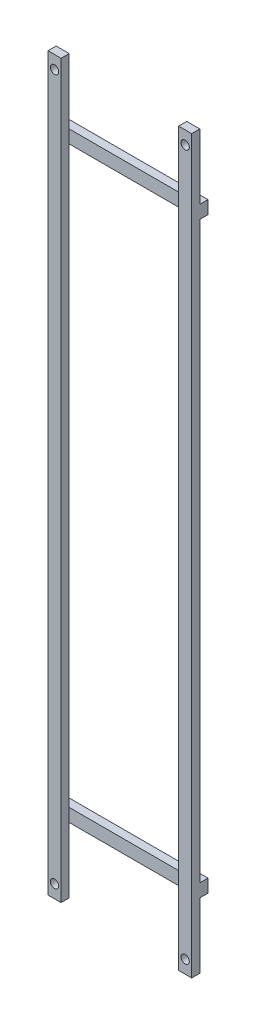
SolidWorks part; units mm, degrees
ref_plane "Front Plane" through (0, 0, 0) normal (0, 0, 1) x (1, 0, 0)
ref_plane "Top Plane" through (0, 0, 0) normal (0, 1, 0) x (1, 0, 0)
ref_plane "Right Plane" through (0, 0, 0) normal (1, 0, 0) x (0, 0, -1)
ref_plane "Plane1" through (45, 0, 0) normal (-1, 0, 0) x (0, -1, 0)
sketch "Sketch1" plane through (45, 0, 0) normal (-1, 0, 0) x (0, -1, 0)
  line L0 (-37.6165, 80) -> (-37.6165, 0)
  line L1 (-37.6165, 0) -> (472.3835, 0)
  line L2 (472.3835, 0) -> (472.3835, 80)
  line L3 (472.3835, 80) -> (-37.6165, 80)
extrude "Boss-Extrude1" add sketch "Sketch1" against normal blind 10
sketch "Sketch2" plane through (45, 0, 0) normal (-1, 0, 0) x (0, 0, 1)
  line L0 (0, -22.3835) -> (0, -412.3835)
  line L1 (0, -412.3835) -> (70, -412.3835)
  line L2 (70, -412.3835) -> (70, -22.3835)
  line L3 (70, -22.3835) -> (0, -22.3835)
extrude "Cut-Extrude1" cut sketch "Sketch2" against normal through all
sketch "Sketch3" plane through (45, 0, 0) normal (-1, 0, 0) x (0, 0, 1)
  line L0 (0, -12.3835) -> (70, -12.3835)
  line L1 (70, -12.3835) -> (70, 37.6165)
  line L2 (70, 37.6165) -> (0, 37.6165)
  line L3 (0, 37.6165) -> (0, -12.3835)
extrude "Cut-Extrude2" cut sketch "Sketch3" against normal through all
sketch "Sketch4" plane through (45, 0, 0) normal (-1, 0, 0) x (0, 0, 1)
  line L0 (70, -22.3835) -> (0, -22.3835)
  line L1 (0, -22.3835) -> (0, -12.3835)
  line L2 (0, -12.3835) -> (70, -12.3835)
  line L3 (70, -12.3835) -> (70, -22.3835)
extrude "Boss-Extrude2" add sketch "Sketch4" along normal blind 100
sketch "Sketch5" plane through (45, 0, 0) normal (-1, 0, 0) x (0, 0, 1)
  line L0 (70, -472.3835) -> (70, -422.3835)
  line L1 (70, -422.3835) -> (0, -422.3835)
  line L2 (0, -422.3835) -> (0, -472.3835)
  line L3 (0, -472.3835) -> (70, -472.3835)
extrude "Cut-Extrude3" cut sketch "Sketch5" against normal through all
sketch "Sketch6" plane through (45, 0, 0) normal (-1, 0, 0) x (0, 0, 1)
  line L0 (70, -422.3835) -> (0, -422.3835)
  line L1 (0, -422.3835) -> (0, -412.3835)
  line L2 (0, -412.3835) -> (70, -412.3835)
  line L3 (70, -412.3835) -> (70, -422.3835)
extrude "Boss-Extrude3" add sketch "Sketch6" along normal blind 100
sketch "Sketch7" plane through (0, 0, 70) normal (0, 0, 1) x (1, 0, 0)
  line L0 (-45, -12.3835) -> (-45, -472.3835)
  line L1 (-45, -472.3835) -> (-55, -472.3835)
  line L2 (-55, -472.3835) -> (-55, -12.3835)
  line L3 (-55, -12.3835) -> (-45, -12.3835)
extrude "Boss-Extrude4" add sketch "Sketch7" along normal blind 10
sketch "Sketch8" plane through (0, -12.3835, 0) normal (0, 1, 0) x (-1, 0, 0)
  line L0 (55, 80) -> (55, 70)
  line L1 (55, 70) -> (45, 70)
  line L2 (45, 70) -> (45, 80)
  line L3 (45, 80) -> (55, 80)
extrude "Boss-Extrude5" add sketch "Sketch8" along normal blind 50
sketch "Sketch9" plane through (0, -22.3835, 0) normal (0, -1, 0) x (1, 0, 0)
  line L0 (45, 0) -> (45, 60)
  line L1 (45, 60) -> (-45, 60)
  line L2 (-45, 60) -> (-45, 0)
  line L3 (-45, 0) -> (45, 0)
extrude "Cut-Extrude4" cut sketch "Sketch9" against normal through all
sketch "Sketch10" plane through (0, -412.3835, 0) normal (0, 1, 0) x (-1, 0, 0)
  line L0 (45, 0) -> (45, 60)
  line L1 (45, 60) -> (-45, 60)
  line L2 (-45, 60) -> (-45, 0)
  line L3 (-45, 0) -> (45, 0)
extrude "Cut-Extrude5" cut sketch "Sketch10" against normal through all
hole_wizard "Hole1" positions "Sketch12" profile "Sketch11" legacy
sketch "Sketch12" plane through (0, 0, 70) normal (0, 0, -1) x (-1, 0, 0)
  point P0 (-50, 27.6165)
  point P1 (50, -462.3835)
sketch "Sketch11" plane through (50, 27.6165, 70) normal (1, 0, 0) x (0, 1, 0)
  line L0 (0, 0) -> (0, 10)
  line L1 (0, 10) -> (3.175, 10)
  line L2 (3.175, 10) -> (3.175, 0)
  line L3 (3.175, 0) -> (0, 0)
  line L4 (0, 110) -> (0, -10) construction
  dimension "Diameter" = 6.35
  dimension "Depth" = 10
hole_wizard "Hole2" positions "Sketch14" profile "Sketch13" legacy
sketch "Sketch14" plane through (0, 0, 80) normal (0, 0, 1) x (1, 0, 0)
  point P0 (50, -462.3835)
  point P1 (-50, 27.6165)
sketch "Sketch13" plane through (50, -462.3835, 80) normal (1, 0, 0) x (0, -1, 0)
  line L0 (0, 0) -> (0, 80)
  line L1 (0, 80) -> (3.175, 80)
  line L2 (3.175, 80) -> (3.175, 0)
  line L3 (3.175, 0) -> (0, 0)
  line L4 (0, 110) -> (0, -10) construction
  dimension "Diameter" = 6.35
  dimension "Depth" = 80
scale "Scale1" scale about centroid uniform scaling yes scale factor 4
sketch "Sketch16" plane through (220, 0, 0) normal (1, 0, 0) x (0, 0, -1)
  line L2 (-81.5788, -1237.3835) -> (-81.5788, -1037.3835) construction
  line L3 (363.7757, 866.3876) -> (-56.5788, 866.3876)
  line L4 (363.7757, 866.3876) -> (363.7757, -1181.0534)
  line L5 (363.7757, -1181.0534) -> (-56.5788, -1181.0534)
  line L6 (-56.5788, 866.3876) -> (-56.5788, -1181.0534)
  line L8 (-81.5788, -997.3835) -> (-81.5788, 562.6165) construction
  line L9 (-610.8485, 823.0413) -> (-106.5788, 823.0413)
  line L10 (-610.8485, 823.0413) -> (-610.8485, -1320.8418)
  line L11 (-610.8485, -1320.8418) -> (-106.5788, -1320.8418)
  line L12 (-106.5788, 823.0413) -> (-106.5788, -1320.8418)
  dimension "D1" = 25
  dimension "D2" = 25
extrude "Cut-Extrude6" cut sketch "Sketch16" against normal blind 600
sketch "Sketch17" plane through (0, 0, 106.5788) normal (0, 0, 1) x (1, 0, 0)
  line L0 (-220, -1237.3835) -> (-220, 802.6165) construction
  line L1 (-220, -217.3835) -> (486.7471, -217.3835)
  line L2 (-220, -217.3835) -> (-220, 873.5026)
  line L3 (-220, 873.5026) -> (486.7471, 873.5026)
  line L4 (486.7471, -217.3835) -> (486.7471, 873.5026)
extrude "Cut-Extrude7" cut sketch "Sketch17" against normal blind 100
sketch "Sketch18" plane through (0, -217.3835, 0) normal (0, 1, 0) x (1, 0, 0)
  line L1 (-220, -81.5788) -> (-180, -81.5788)
  line L2 (-220, -81.5788) -> (-220, -106.5788)
  line L3 (-220, -106.5788) -> (-180, -106.5788)
  line L4 (-180, -81.5788) -> (-180, -106.5788)
  line L5 (180, -81.5788) -> (220, -81.5788)
  line L6 (180, -81.5788) -> (180, -106.5788)
  line L7 (180, -106.5788) -> (220, -106.5788)
  line L8 (220, -81.5788) -> (220, -106.5788)
extrude "Boss-Extrude6" add sketch "Sketch18" along normal blind 100
sketch "Sketch20" plane through (0, 0, 106.5788) normal (0, 0, 1) x (1, 0, 0)
  line L0 (-391.2787, -117.3835) -> (585.6528, -117.3835) construction
  line L1 (-220, -117.3835) -> (-180, -117.3835)
  line L2 (-220, 1002.6165) -> (-220, -117.3835)
  line L4 (-180, 1002.6165) -> (-180, -117.3835)
  line L5 (180, -117.3835) -> (220, -117.3835)
  line L6 (180, 1002.6165) -> (180, -117.3835)
  line L8 (220, 1002.6165) -> (220, -117.3835)
  line L9 (180, 1002.6165) -> (220, 1002.6165)
  line L10 (-220, 1002.6165) -> (-180, 1002.6165)
  circle A2 centre (200, 962.6165) radius 12.7
  circle A3 centre (-200, 962.6165) radius 12.7
extrude "Boss-Extrude9" add sketch "Sketch20" against normal blind 25
sketch "Sketch21" plane through (0, 0, 81.5788) normal (0, 0, -1) x (-1, 0, 0)
  line L1 (-389.8468, -117.3835) -> (638.2169, -117.3835) construction
  line L2 (220, 762.6165) -> (220, 802.6165)
  line L7 (-220, 802.6165) -> (220, 802.6165)
  line L8 (-220, 762.6165) -> (-220, 802.6165)
  line L9 (-220, 762.6165) -> (220, 762.6165)
extrude "Boss-Extrude10" add sketch "Sketch21" along normal blind 25
